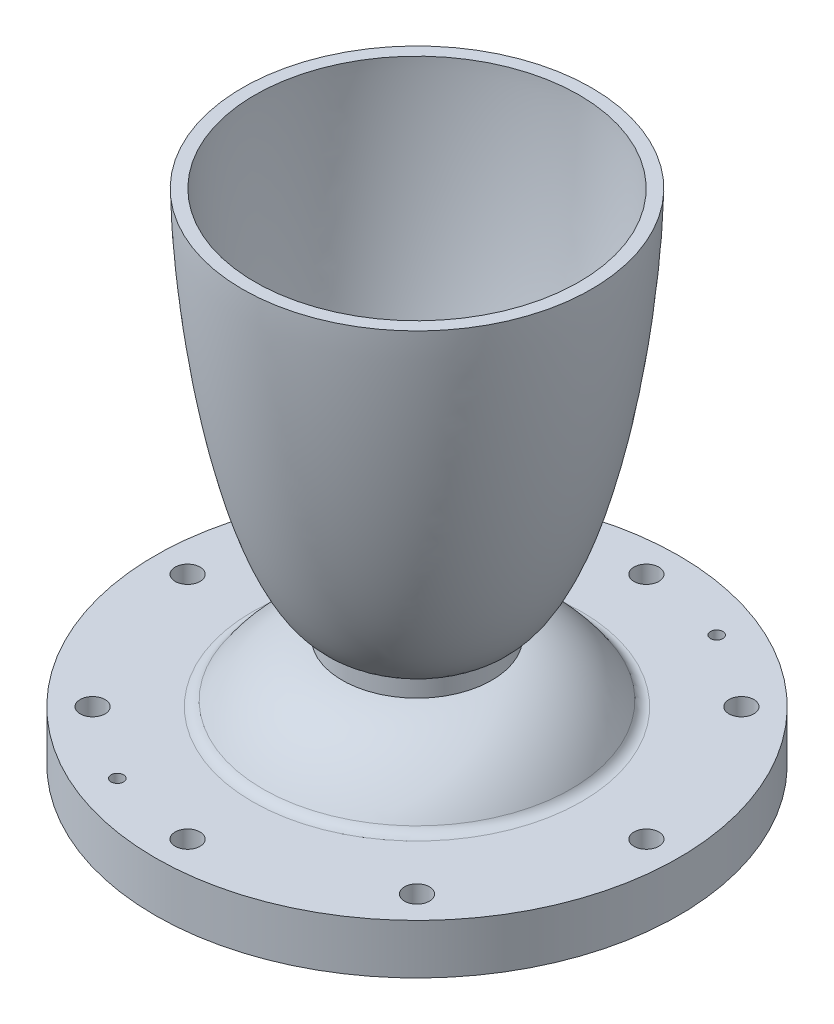
SolidWorks part; units mm, degrees
ref_plane "Front Plane" through (0, 0, 0) normal (0, 0, 1) x (1, 0, 0)
ref_plane "Top Plane" through (0, 0, 0) normal (0, 1, 0) x (1, 0, 0)
ref_plane "Right Plane" through (0, 0, 0) normal (1, 0, 0) x (0, 0, -1)
sketch "Sketch1" plane through (0, 0, 0) normal (0, 0, 1) x (1, 0, 0)
  line L0 (0, 0) -> (0, 127) construction
  line L1 (0, 0) -> (-76.2, 0) construction
  line L2 (0, 25.4) -> (-76.2, 25.4) construction
  line L3 (0, 34.925) -> (-76.2, 34.925) construction
  line L4 (0, 127) -> (-76.2, 127) construction
  line L5 (-41.275, 0) -> (-41.275, 127) construction
  line L6 (-9.525, 0) -> (-9.525, 127) construction
  line L7 (-9.5179, 29.8543) -> (-9.5179, 31.0043)
  line L11 (-41.275, 0) -> (-66.675, 0)
  line L12 (-66.675, 0) -> (-66.675, 12.7)
  line L13 (-44.45, 127) -> (-41.275, 127)
  line L14 (-19.05, 28.0421) -> (-19.05, 32.4773)
  line L15 (-66.675, 12.7) -> (-40.1329, 12.7)
  arc A0 (-9.5179, 29.8543) -> (-13.6663, 25.1315) centre (-14.2804, 29.8543) cw
  arc A1 (-12.6773, 35.4889) -> (-9.5179, 31.0043) centre (-14.2804, 31.0043) cw
  spline S0 degree 4 poles (-41.275, 0) (-41.274, 0.0486) (-41.2703, 0.1458) (-41.2499, 0.4207) (-41.1845, 0.9521) (-41.0457, 1.7182) (-40.8031, 2.7106) (-40.4714, 3.7959) (-40.0739, 4.8928) (-39.5825, 6.0748) (-38.9093, 7.4952) (-38.0132, 9.1298) (-36.851, 10.946) (-35.4547, 12.8169) (-33.9314, 14.5858) (-32.2904, 16.2459) (-30.5401, 17.7904) (-28.6887, 19.2123) (-26.7446, 20.5043) (-24.7162, 21.6597) (-22.6125, 22.6717) (-20.4432, 23.534) (-18.4963, 24.1525) (-16.7999, 24.5824) (-15.5134, 24.8436) (-14.652, 24.992) (-13.9295, 25.0983) (-13.3539, 25.1729) (-12.7691, 25.2371) (-12.1975, 25.2908) (-11.6002, 25.334) (-11.0462, 25.3667) (-10.5221, 25.3848) (-10.2205, 25.3937) (-9.8178, 25.3983) (-9.4782, 25.4019) (-8.766, 25.3965) (-7.8642, 25.3656) (-6.771, 25.2903) (-5.943, 25.2058) (-5.4011, 25.137) (-5.1262, 25.0995) knots 0 0 0 0 0 0.004015 0.00803 0.022747 0.044178 0.068247 0.092317 0.116386 0.140456 0.173884 0.222023 0.270162 0.318301 0.36644 0.414579 0.462719 0.510858 0.558997 0.607136 0.655275 0.703414 0.751553 0.775623 0.799692 0.811727 0.823762 0.835797 0.847831 0.859866 0.871901 0.883936 0.89597 0.899251 0.902531 0.909092 0.931819 0.954546 0.977273 1 1 1 1 1 construction
  spline S1 degree 4 poles (-41.275, 0) (-41.274, 0.0486) (-41.2703, 0.1458) (-41.2499, 0.4207) (-41.1845, 0.9521) (-41.0457, 1.7182) (-40.8031, 2.7106) (-40.4714, 3.7959) (-40.0739, 4.8928) (-39.5825, 6.0748) (-38.9093, 7.4952) (-38.0132, 9.1298) (-36.851, 10.946) (-35.4547, 12.8169) (-33.9314, 14.5858) (-32.2904, 16.2459) (-30.5401, 17.7904) (-28.6887, 19.2123) (-26.7446, 20.5043) (-24.7162, 21.6597) (-22.6125, 22.6717) (-20.4432, 23.534) (-18.4963, 24.1525) (-16.7999, 24.5824) (-15.5134, 24.8436) (-14.6582, 24.9909) (-14.0865, 25.0752) (-13.8044, 25.1136) (-13.6663, 25.1315) knots 0 0 0 0 0 0.004015 0.00803 0.022747 0.044178 0.068247 0.092317 0.116386 0.140456 0.173884 0.222023 0.270162 0.318301 0.36644 0.414579 0.462719 0.510858 0.558997 0.607136 0.655275 0.703414 0.751553 0.775623 0.799692 0.811727 0.823244 0.823244 0.823244 0.823244 0.823244
  spline S2 degree 4 poles (-41.275, 127) (-41.2689, 126.1614) (-41.223, 124.4846) (-41.0734, 121.0785) (-40.7228, 115.949) (-40.1705, 109.9396) (-39.3608, 103.0591) (-38.3822, 96.2006) (-37.2306, 89.369) (-35.8956, 82.5706) (-34.3591, 75.8148) (-32.5938, 69.1146) (-30.5585, 62.4908) (-28.1913, 55.9764) (-25.6831, 50.2918) (-23.1258, 45.5925) (-20.7112, 42.0555) (-18.7203, 39.6859) (-17.0528, 38.1035) (-15.7469, 37.1002) (-14.7707, 36.4765) (-14.0774, 36.0905) (-13.4074, 35.7704) (-12.7662, 35.5114) (-12.1434, 35.3055) (-11.5442, 35.1486) (-11.0256, 35.048) (-10.6005, 34.9876) (-10.2387, 34.9525) (-9.9404, 34.9337) (-9.6298, 34.9237) (-9.3404, 34.9245) (-8.9827, 34.9383) (-8.6161, 34.9673) (-8.2594, 35.0109) (-7.9015, 35.0689) (-7.453, 35.1595) (-6.8882, 35.3045) (-6.2156, 35.5254) (-5.3966, 35.8667) (-4.53, 36.3129) (-3.8846, 36.7116) (-3.4379, 37.0182) (-3.2182, 37.1769) knots 0 0 0 0 0 0.030812 0.061623 0.12525 0.188877 0.252504 0.316131 0.379757 0.443384 0.507011 0.570638 0.634265 0.697892 0.761519 0.798698 0.830511 0.855004 0.875012 0.882966 0.890919 0.897534 0.90415 0.910229 0.916309 0.921611 0.926913 0.929564 0.932215 0.934867 0.937518 0.940824 0.944131 0.947438 0.950745 0.954114 0.957484 0.964223 0.97216 0.980096 0.990048 1 1 1 1 1 construction
  spline S3 degree 4 poles (-41.275, 127) (-41.2689, 126.1614) (-41.223, 124.4846) (-41.0734, 121.0785) (-40.7228, 115.949) (-40.1705, 109.9396) (-39.3608, 103.0591) (-38.3822, 96.2006) (-37.2306, 89.369) (-35.8956, 82.5706) (-34.3591, 75.8148) (-32.5938, 69.1146) (-30.5585, 62.4908) (-28.1913, 55.9764) (-25.6831, 50.2918) (-23.1258, 45.5925) (-20.7112, 42.0555) (-18.7203, 39.6859) (-17.0528, 38.1035) (-15.7469, 37.1002) (-14.7707, 36.4765) (-14.0774, 36.0905) (-13.4648, 35.7979) (-13.0376, 35.6216) (-12.7733, 35.5232) (-12.6773, 35.4889) knots 0 0 0 0 0 0.030812 0.061623 0.12525 0.188877 0.252504 0.316131 0.379757 0.443384 0.507011 0.570638 0.634265 0.697892 0.761519 0.798698 0.830511 0.855004 0.875012 0.882966 0.890919 0.897534 0.90415 0.907893 0.907893 0.907893 0.907893 0.907893
  spline S4 degree 4 poles (-44.45, 127) (-44.444, 126.0899) (-44.3997, 124.27) (-44.2562, 120.6046) (-43.9212, 115.0986) (-43.395, 108.6661) (-42.6246, 101.3148) (-41.6912, 93.9824) (-40.5889, 86.6733) (-39.3055, 79.3937) (-37.8196, 72.1526) (-36.0989, 64.963) (-34.093, 57.8471) (-31.7662, 50.972) (-29.315, 45.1286) (-26.8381, 40.4693) (-24.5703, 37.1783) (-22.7831, 35.133) (-21.3073, 33.8365) (-20.1932, 33.0738) (-19.3831, 32.6276) (-18.8014, 32.3576) (-18.24, 32.1443) (-17.7056, 31.9828) (-17.2391, 31.8782) (-16.8521, 31.815) (-16.5271, 31.7785) (-16.26, 31.759) (-15.9995, 31.7494) (-15.7743, 31.7491) (-15.5273, 31.7574) (-15.2825, 31.7735) (-14.9713, 31.8052) (-14.5939, 31.8625) (-14.1334, 31.9598) (-13.603, 32.1134) (-13.0484, 32.3164) (-12.4762, 32.5733) (-11.8579, 32.9033) (-11.2026, 33.3155) (-10.7145, 33.6712) (-10.3753, 33.941) (-10.2085, 34.0795) knots 0 0 0 0 0 0.033161 0.066322 0.133645 0.200968 0.268291 0.335614 0.402937 0.47026 0.537583 0.604906 0.672229 0.739552 0.80187 0.835532 0.864104 0.884898 0.900578 0.906888 0.913199 0.918565 0.923931 0.92874 0.933549 0.935917 0.938286 0.940654 0.943023 0.945188 0.947354 0.94952 0.951685 0.956526 0.961366 0.966591 0.971816 0.978012 0.984208 0.992104 1 1 1 1 1 construction
  spline S5 degree 4 poles (-44.45, 127) (-44.444, 126.0899) (-44.3997, 124.27) (-44.2562, 120.6046) (-43.9212, 115.0986) (-43.395, 108.6661) (-42.6246, 101.3148) (-41.6912, 93.9824) (-40.5889, 86.6733) (-39.3055, 79.3937) (-37.8196, 72.1526) (-36.0989, 64.963) (-34.093, 57.8471) (-31.7662, 50.972) (-29.315, 45.1286) (-26.8381, 40.4693) (-24.5703, 37.1783) (-22.7831, 35.133) (-21.3073, 33.8365) (-20.1947, 33.0748) (-19.5153, 32.7005) (-19.2058, 32.5488) (-19.05, 32.4773) knots 0 0 0 0 0 0.033161 0.066322 0.133645 0.200968 0.268291 0.335614 0.402937 0.47026 0.537583 0.604906 0.672229 0.739552 0.80187 0.835532 0.864104 0.884898 0.900578 0.906888 0.913134 0.913134 0.913134 0.913134 0.913134
  spline S6 degree 4 poles (-44.45, 0) (-44.4483, 0.0878) (-44.4412, 0.2631) (-44.4148, 0.6073) (-44.3577, 1.1188) (-44.2459, 1.8792) (-43.9954, 3.1854) (-43.5388, 4.9726) (-42.7934, 7.2108) (-41.7462, 9.7001) (-40.5024, 12.1356) (-39.0839, 14.4736) (-37.4964, 16.7005) (-35.7433, 18.7998) (-33.8284, 20.7529) (-31.7553, 22.5382) (-29.7656, 23.9638) (-27.9592, 25.046) (-26.3894, 25.8454) (-25.0889, 26.4204) (-23.8141, 26.9067) (-22.5079, 27.3232) (-21.1926, 27.6671) (-19.8391, 27.9358) (-18.6772, 28.1034) (-17.6209, 28.198) (-16.8541, 28.2423) (-16.1779, 28.2573) (-15.7814, 28.2588) (-15.3336, 28.2524) (-14.9681, 28.2412) (-14.522, 28.2203) (-13.9756, 28.184) (-13.3447, 28.1252) (-12.7091, 28.0466) (-12.1672, 27.965) (-11.8037, 27.9029) (-11.6227, 27.8699) (-11.5324, 27.853) knots 0 0 0 0 0 0.007303 0.014606 0.028717 0.042828 0.071253 0.125257 0.182105 0.238953 0.295801 0.352649 0.409497 0.466345 0.523193 0.580041 0.636889 0.669796 0.69822 0.726644 0.755068 0.783492 0.811916 0.84034 0.868764 0.882976 0.897188 0.909091 0.916625 0.924158 0.931692 0.939226 0.954293 0.96936 0.98468 0.99234 1 1 1 1 1 construction
  spline S7 degree 4 poles (-40.1329, 12.7) (-40.0458, 12.8498) (-39.6106, 13.5874) (-38.7877, 14.8891) (-37.4964, 16.7005) (-35.7433, 18.7998) (-33.8284, 20.7529) (-31.7553, 22.5382) (-29.7656, 23.9638) (-27.9592, 25.046) (-26.3894, 25.8454) (-25.0889, 26.4204) (-23.8141, 26.9067) (-22.5079, 27.3232) (-21.1926, 27.6671) (-20.1469, 27.8747) (-19.4488, 27.987) (-19.0806, 28.0379) (-19.05, 28.0421) knots 0.281378 0.281378 0.281378 0.281378 0.281378 0.295801 0.352649 0.409497 0.466345 0.523193 0.580041 0.636889 0.669796 0.69822 0.726644 0.755068 0.783492 0.811916 0.84034 0.842914 0.842914 0.842914 0.842914 0.842914
  dimension "D9" = 4.7625
  dimension "D10" = 4.7625
  dimension "D1" = 127
  dimension "D2" = 76.2
  dimension "D3" = 41.275
  dimension "D4" = 25.4
  dimension "D5" = 9.525
  dimension "D6" = 9.525
  dimension "D7" = 66.675
  dimension "D8" = 12.7
revolve "Main Revolve" add sketch "Sketch1" angle 360 about L0
fillet "Converging Fillet" radius 3.175 1 edges at (0, 12.7, -40.1329)
sketch "Sketch for Bolt Holes" plane through (0, 12.7, 0) normal (0, 1, 0) x (1, 0, 0)
  circle A0 centre (0, 0) radius 58.42
  circle A1 centre (-58.42, 0) radius 3.175
  circle A2 centre (-41.3092, 41.3092) radius 3.175
  circle A3 centre (0, 58.42) radius 3.175
  circle A4 centre (41.3092, 41.3092) radius 3.175
  circle A5 centre (58.42, 0) radius 3.175
  circle A6 centre (41.3092, -41.3092) radius 3.175
  circle A7 centre (0, -58.42) radius 3.175
  circle A8 centre (-41.3092, -41.3092) radius 3.175
  point P22 (0, 0)
  dimension "D1" = 116.84
  dimension "D2" = 6.35
  dimension "D3" = 8
hole_wizard "Bolt Holes" positions "Sketch3" profile "Sketch4" hole size "1/4" standard "ANSI Inch"
sketch "Sketch3" plane through (0, 12.7, 0) normal (0, 1, 0) x (1, 0, 0)
  point P0 (-58.42, 0)
  point P3 (-41.3092, 41.3092)
  point P6 (0, 58.42)
  point P9 (41.3092, 41.3092)
  point P12 (58.42, 0)
  point P15 (41.3092, -41.3092)
  point P18 (0, -58.42)
  point P21 (-41.3092, -41.3092)
sketch "Sketch4" plane through (-58.42, 12.7, 0) normal (1, 0, 0) x (0, 0, 1)
  line L0 (0, 0) -> (0, 14.6077)
  line L1 (0, 14.6077) -> (3.175, 12.7)
  line L2 (3.175, 12.7) -> (3.175, 0)
  line L5 (3.175, 0) -> (0, 0)
  line L10 (0, 14.6077) -> (-3.175, 12.7) construction
  line L11 (0, -6.35) -> (0, 107.95) construction
  dimension "Hole Dia." = 6.35
  dimension "Hole Depth" = 12.7
  dimension "Drill Angle" = 118
sketch "Sketch for Pin Holes" plane through (0, 0, 0) normal (0, -1, 0) x (1, 0, 0)
  line L0 (0, 0) -> (0, -69.4939) construction
  line L1 (0, 0) -> (29.6148, -71.4963) construction
  circle A0 centre (0, 0) radius 58.42
  circle A1 centre (22.3564, -53.973) radius 3.175
  circle A2 centre (-22.3564, 53.973) radius 3.175
  point P11 (0, 0)
  dimension "D2" = 6.35
  dimension "D1" = 22.5
  dimension "D3" = 2
hole_wizard "Pin Holes" positions "Sketch6" profile "Sketch7" legacy
sketch "Sketch6" plane through (0, 0, 0) normal (0, -1, 0) x (-1, 0, 0)
  point P0 (-22.3564, 53.973)
  point P3 (22.3564, -53.973)
sketch "Sketch7" plane through (22.3564, 0, -53.973) normal (1, 0, 0) x (0, 0, -1)
  line L0 (0, 0) -> (0, 100)
  line L1 (0, 100) -> (1.5875, 100)
  line L2 (1.5875, 100) -> (1.5875, 6.35)
  line L3 (1.5875, 6.35) -> (3.175, 6.35)
  line L4 (3.175, 6.35) -> (3.175, 0)
  line L5 (3.175, 0) -> (0, 0)
  line L6 (0, 110) -> (0, -10) construction
  dimension "Diameter" = 3.175
  dimension "Depth" = 100
  dimension "C-Bore Diameter" = 6.35
  dimension "C-Bore Depth" = 6.35
